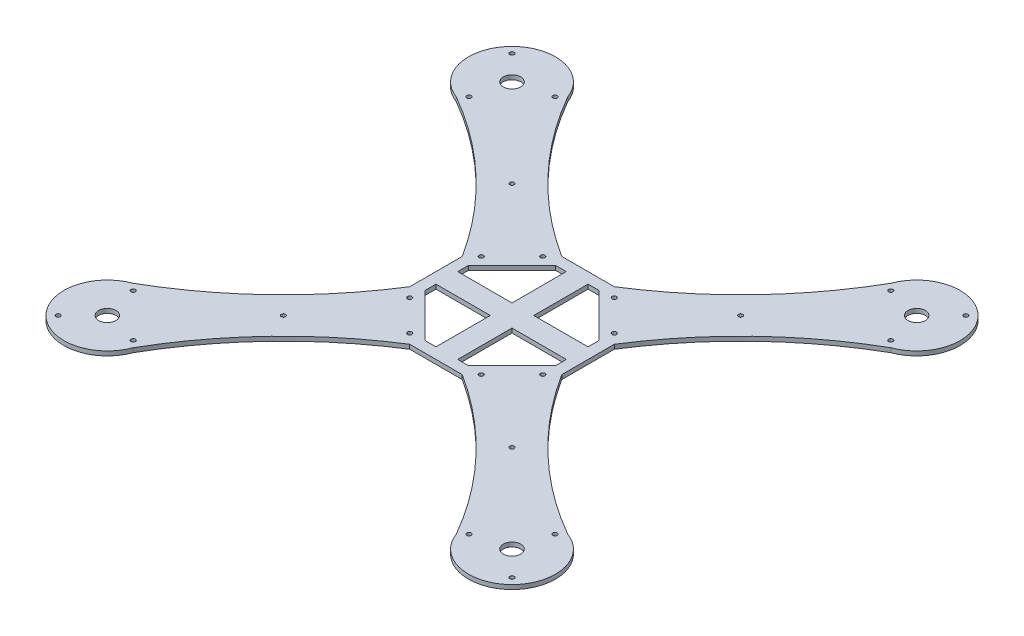
SolidWorks part; units mm, degrees
material "6061-T6 (SS)"
ref_plane "Front Plane" through (0, 0, 0) normal (0, 0, 1) x (1, 0, 0)
ref_plane "Top Plane" through (0, 0, 0) normal (0, 1, 0) x (1, 0, 0)
ref_plane "Right Plane" through (0, 0, 0) normal (1, 0, 0) x (0, 0, -1)
sketch "Sketch2" plane through (0, 0, 0) normal (0, 1, 0) x (1, 0, 0)
  line L0 (74.3315, 99.9895) -> (99.9895, 74.3315) construction
  line L1 (0, 0) -> (35, 0)
  line L2 (0, 0) -> (0, 35)
  line L3 (0, 35) -> (12.0711, 35)
  line L4 (35, 0) -> (35, 12.0711)
  line L5 (12.0711, 35) -> (35, 12.0711) construction
  line L6 (16.4645, 30.6066) -> (30.6066, 16.4645) construction
  line L7 (-88.2363, 193.413) -> (193.413, -88.2363) construction
  line L8 (5, 30) -> (5, 5)
  line L9 (5, 5) -> (30, 5)
  line L10 (23.5355, 23.5355) -> (107.2539, 107.2539) construction
  line L11 (30, 5) -> (30, 10)
  line L12 (30, 10) -> (10, 30)
  line L13 (10, 30) -> (5, 30)
  arc A0 (99.9895, 74.3315) -> (74.3315, 99.9895) centre (93.1118, 93.1118) ccw
  arc A1 (99.9895, 74.3315) -> (35, 12.0711) centre (193.413, -88.2363) ccw
  arc A2 (74.3315, 99.9895) -> (12.0711, 35) centre (-88.2363, 193.413) cw
  circle A3 centre (93.1118, 93.1118) radius 4
  circle A4 centre (52.5884, 52.5884) radius 1
  circle A5 centre (16.4645, 30.6066) radius 1
  circle A6 centre (30.6066, 16.4645) radius 1
  circle A7 centre (97.06, 77.261) radius 1
  circle A8 centre (77.261, 97.06) radius 1
  circle A9 centre (104.4255, 104.4255) radius 1
  point P26 (6.0355, 35)
  point P28 (87.1605, 87.1605)
  dimension "D5" = 40
  dimension "D6" = 187.5
  dimension "D7" = 131.6799
  dimension "D10" = 8
  dimension "D9" = 2
  dimension "D12" = 2
  dimension "D13" = 2
  dimension "D14" = 2
  dimension "D15" = 2
  dimension "D24" = 2
  dimension "D3" = 35
  dimension "D4" = 90
  dimension "D8" = 45
  dimension "D11" = 35
  dimension "D16" = 10
  dimension "D17" = 10
  dimension "D18" = 14
  dimension "D19" = 14
  dimension "D20" = 5
  dimension "D21" = 5
  dimension "D22" = 5
  dimension "D23" = 5
  dimension "D25" = 16
  dimension "D26" = 5
  dimension "D27" = 5
extrude "Boss-Extrude1" add sketch "Sketch2" along normal blind 2
pattern_circular "CirPattern1" count 4 over 360 about axis through (0, 0, 0) along (0, 1, 0) of "Boss-Extrude1"
sketch "Sketch3" plane through (0, 0, 0) normal (0, -1, 0) x (-1, 0, 0)
  line L0 (-30.6066, -16.4645) -> (-16.4645, -30.6066) construction
  line L1 (-30.6066, 16.4645) -> (-16.4645, 30.6066) construction
  line L2 (30.6066, 16.4645) -> (16.4645, 30.6066) construction
  line L3 (30.6066, -16.4645) -> (16.4645, -30.6066) construction
  point P14 (23.5355, -23.5355)
  point P17 (23.5355, 23.5355)
  point P18 (-23.5355, 23.5355)
  point P19 (-23.5355, -23.5355)
